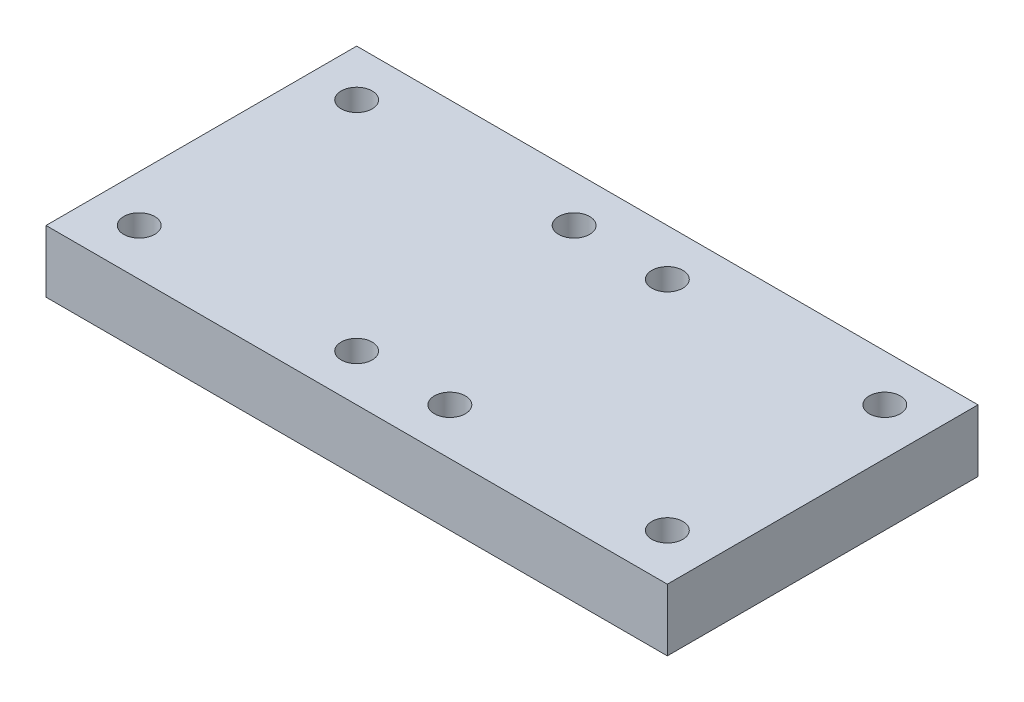
SolidWorks part; units mm, degrees
ref_plane "Front Plane" through (0, 0, 0) normal (0, 0, 1) x (1, 0, 0)
ref_plane "Top Plane" through (0, 0, 0) normal (0, 1, 0) x (1, 0, 0)
ref_plane "Right Plane" through (0, 0, 0) normal (1, 0, 0) x (0, 0, -1)
sketch "Sketch1" plane through (0, 0, 0) normal (0, 1, 0) x (1, 0, 0)
  line L1 (-50, 25) -> (50, 25)
  line L2 (-50, 25) -> (-50, -25)
  line L3 (-50, -25) -> (50, -25)
  line L4 (50, 25) -> (50, -25)
  line L5 (-50, 25) -> (50, -25) construction
  line L6 (-50, -25) -> (50, 25) construction
  circle A0 centre (-42.5, 17.5) radius 2.5
  circle A1 centre (42.5, 17.5) radius 2.5
  circle A2 centre (42.5, -17.5) radius 2.5
  circle A3 centre (-42.5, -17.5) radius 2.5
  point P0 (0, 0)
  dimension "D3" = 5
  dimension "D1" = 100
  dimension "D2" = 50
  dimension "D4" = 85
  dimension "D5" = 35
  dimension "D6" = 7.5
  dimension "D7" = 7.5
extrude "Boss-Extrude1" add sketch "Sketch1" along normal blind 10
sketch "Sketch3" plane through (0, 10, 0) normal (0, 1, 0) x (1, 0, 0)
  line L0 (-50, -25) -> (50, -25) construction
  line L2 (-50, 25) -> (-50, -25) construction
  circle A0 centre (-7.5, 17.5) radius 2.5
  circle A1 centre (7.5, 17.5) radius 2.5
  circle A2 centre (7.5, -17.5) radius 2.5
  circle A3 centre (-7.5, -17.5) radius 2.5
  dimension "D1" = 5
  dimension "D2" = 35
  dimension "D3" = 15
  dimension "D4" = 7.5
  dimension "D5" = 42.5
extrude "Cut-Extrude1" cut sketch "Sketch3" against normal blind 10
